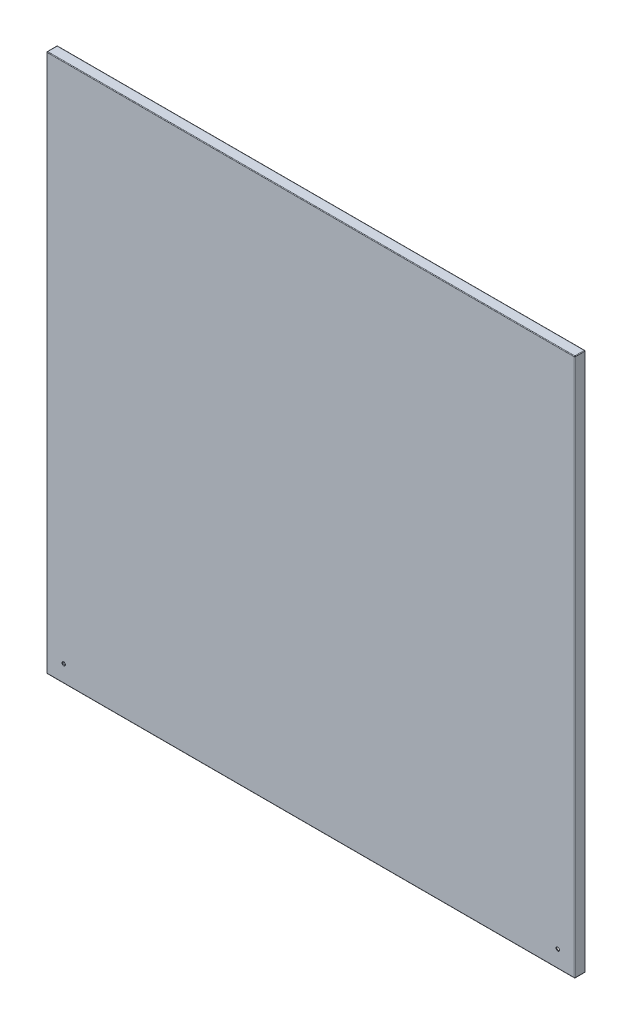
SolidWorks part; units mm, degrees
ref_plane "前视基准面" through (0, 0, 0) normal (0, 0, 1) x (1, 0, 0)
ref_plane "上视基准面" through (0, 0, 0) normal (0, 1, 0) x (1, 0, 0)
ref_plane "右视基准面" through (0, 0, 0) normal (1, 0, 0) x (0, 0, -1)
sketch "草图1" plane through (0, 0, 0) normal (0, 0, 1) x (1, 0, 0)
  line L1 (450, -459) -> (-450, -459)
  line L2 (450, -459) -> (450, 459)
  line L3 (450, 459) -> (-450, 459)
  line L4 (-450, -459) -> (-450, 459)
  line L5 (450, -459) -> (-450, 459) construction
  line L6 (450, 459) -> (-450, -459) construction
  point P0 (0, 0)
  dimension "D1" = 900
  dimension "D2" = 918
extrude "凸台-拉伸1" add sketch "草图1" along normal blind 1.5
sketch "草图2" plane through (0, 0, 0) normal (0, 0, -1) x (-1, 0, 0)
  line L1 (-450, -459) -> (450, -459)
  line L2 (-450, -459) -> (-450, 459)
  line L3 (-450, 459) -> (450, 459)
  line L4 (450, -459) -> (450, 459)
  line L5 (-450, -459) -> (450, 459) construction
  line L6 (-450, 459) -> (450, -459) construction
  line L7 (-448.5, -457.5) -> (448.5, -457.5)
  line L8 (-448.5, -457.5) -> (-448.5, 457.5)
  line L9 (-448.5, 457.5) -> (448.5, 457.5)
  line L10 (448.5, -457.5) -> (448.5, 457.5)
  line L11 (-448.5, -457.5) -> (448.5, 457.5) construction
  line L12 (-448.5, 457.5) -> (448.5, -457.5) construction
  point P0 (0, 0)
  point P7 (0, 0)
  dimension "D1" = 1.5
  dimension "D2" = 1.5
extrude "凸台-拉伸2" add sketch "草图2" along normal blind 15
sketch "草图3" plane through (0, 0, -15) normal (0, 0, -1) x (-1, 0, 0)
  line L1 (-450, -459) -> (450, -459)
  line L2 (-450, -459) -> (-450, 459)
  line L3 (-450, 459) -> (450, 459)
  line L4 (450, -459) -> (450, 459)
  line L5 (-450, -459) -> (450, 459) construction
  line L6 (-450, 459) -> (450, -459) construction
  line L7 (-435, -449) -> (435, -449)
  line L8 (-435, -449) -> (-435, 449)
  line L9 (-435, 449) -> (435, 449)
  line L10 (435, -449) -> (435, 449)
  line L11 (-435, -449) -> (435, 449) construction
  line L12 (-435, 449) -> (435, -449) construction
  point P0 (0, 0)
  point P7 (0, 0)
  dimension "D1" = 10
  dimension "D2" = 15
extrude "凸台-拉伸3" add sketch "草图3" along normal blind 1.5
sketch "草图6" plane through (0, 0, 1.5) normal (0, 0, 1) x (1, 0, 0)
  line L0 (0, -459) -> (0, 459) construction
  line L1 (-450, -459) -> (450, -459) construction
  line L2 (450, 459) -> (-450, 459) construction
  line L3 (-450, 459) -> (-450, -459) construction
  circle A0 centre (-421, -430) radius 3
  circle A1 centre (421, -430) radius 3
  dimension "D3" = 6
  dimension "D1" = 29
  dimension "D2" = 29
extrude "切除-拉伸1" cut sketch "草图6" against normal through all
fillet "圆角1" radius 1 12 edges at (0, -459, -16.5) (450, 0, -16.5) (0, 459, -16.5) (-450, 459, -7.5) (-450, 0, -16.5) (450, -459, -7.5) (-450, -459, -7.5) (-450, 0, 1.5) (0, -459, 1.5) (0, 459, 1.5) (450, 0, 1.5) (450, 459, -7.5)
